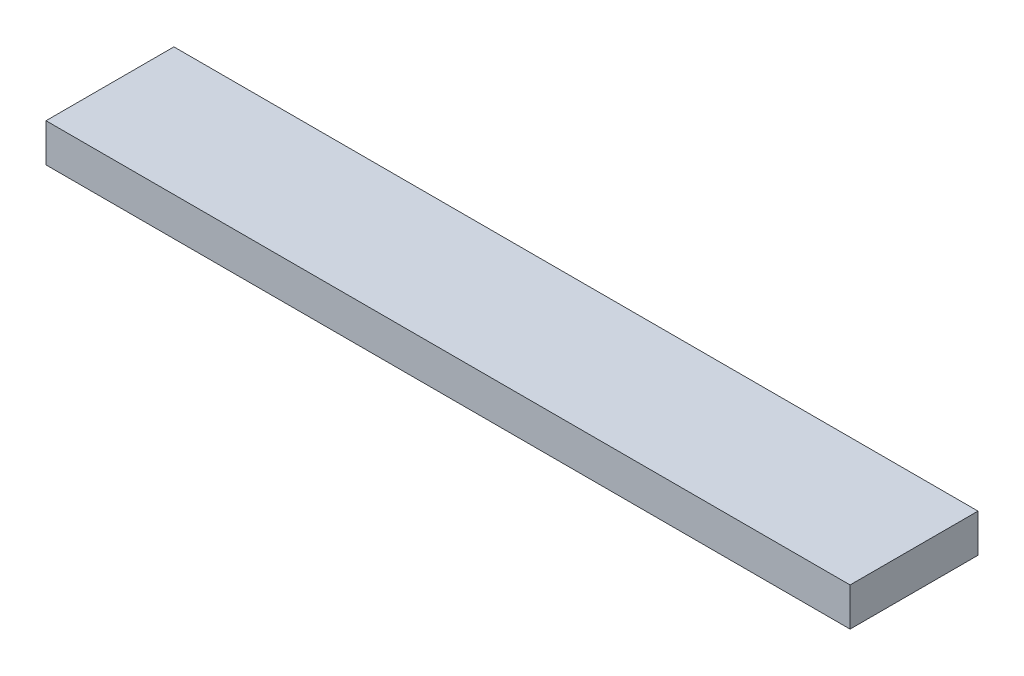
SolidWorks part; units mm, degrees
ref_plane "Plan de face" through (0, 0, 0) normal (0, 0, 1) x (1, 0, 0)
ref_plane "Plan de dessus" through (0, 0, 0) normal (0, 1, 0) x (1, 0, 0)
ref_plane "Plan de droite" through (0, 0, 0) normal (1, 0, 0) x (0, 0, -1)
sketch "Esquisse1" plane through (0, 0, 0) normal (0, 0, 1) x (1, 0, 0)
  line L0 (261, -20) -> (261, 36) construction
  line L1 (-201, 36) -> (261, 36)
  line L2 (-201, 36) -> (-201, 14)
  line L3 (-201, 14) -> (261, 14)
  line L4 (261, 36) -> (261, 14)
  dimension "D1" = 22
extrude "Boss.-Extru.1" add sketch "Esquisse1" along normal up to surface (73.5 mm away) contours L3 L4 L1 L2
